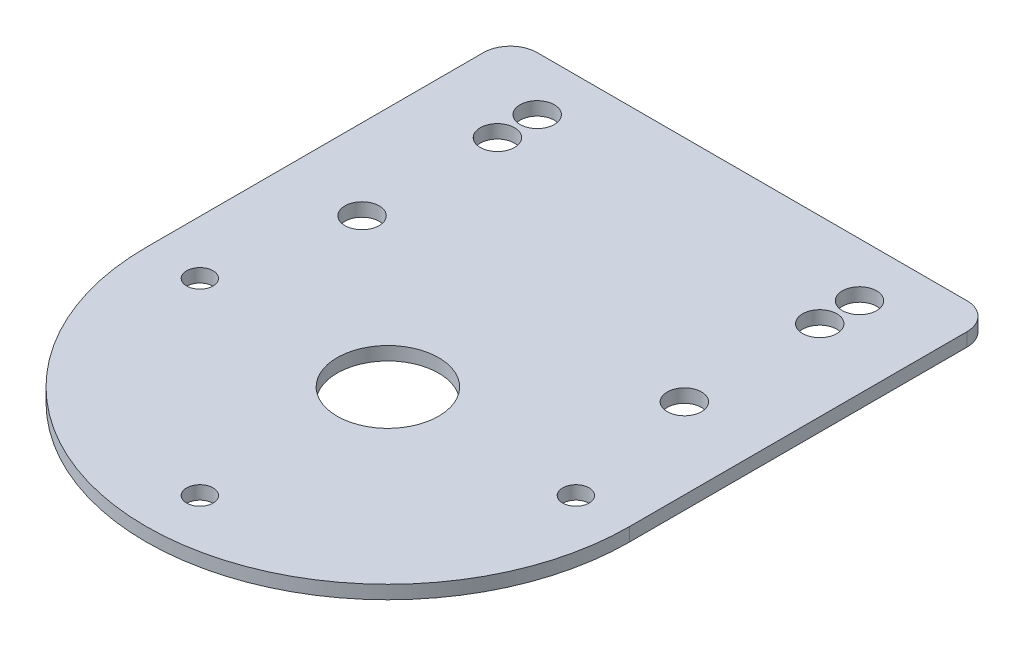
SolidWorks part; units mm, degrees
ref_plane "Front Plane" through (0, 0, 0) normal (0, 0, 1) x (1, 0, 0)
ref_plane "Top Plane" through (0, 0, 0) normal (0, 1, 0) x (1, 0, 0)
ref_plane "Right Plane" through (0, 0, 0) normal (1, 0, 0) x (0, 0, -1)
sketch "Sketch1" plane through (0, 0, 0) normal (0, 1, 0) x (1, 0, 0)
  line L0 (-28.575, 0) -> (-28.575, 39.875)
  line L1 (-25.4, 43.05) -> (25.4, 43.05)
  line L2 (28.575, 39.875) -> (28.575, 0)
  line L3 (0, 0) -> (0, 24) construction
  line L4 (-28.575, 25.4) -> (28.575, 25.4) construction
  line L5 (-19.05, 32) -> (19.05, 16) construction
  circle A0 centre (0, 0) radius 6
  circle A1 centre (0, 0) radius 13 construction
  arc A6 (-28.575, 0) -> (28.575, 0) centre (0, 0) ccw
  circle A7 centre (0, 0) radius 20 construction
  circle A8 centre (0, 0) radius 22.225 construction
  circle A9 centre (-22.225, 0) radius 1.5625
  circle A10 centre (0, -22.225) radius 1.5625
  circle A11 centre (22.225, 0) radius 1.5625
  circle A12 centre (-19.05, 16) radius 2.025
  circle A13 centre (19.05, 16) radius 2.025
  circle A14 centre (19.05, 32) radius 2.025
  circle A15 centre (-19.05, 32) radius 2.025
  circle A16 centre (-19.05, 36.7) radius 2.025
  circle A17 centre (19.05, 36.7) radius 2.025
  arc A18 (25.4, 43.05) -> (28.575, 39.875) centre (25.4, 39.875) cw
  arc A19 (-28.575, 39.875) -> (-25.4, 43.05) centre (-25.4, 39.875) cw
  point P15 (0, 0)
  point P24 (0, 0)
  point P30 (0, 22.225)
  dimension "D1" = 12
  dimension "D2" = 3.125
  dimension "D3" = 26
  dimension "D5" = 57.15
  dimension "D6" = 40
  dimension "D7" = 44.45
  dimension "D11" = 4.05
  dimension "D19" = 3.175
  dimension "D9" = 24
  dimension "D14" = 19.05
  dimension "D15" = 16
  dimension "D17" = 19.05
  dimension "D18" = 6.35
  dimension "D4" = 12.7
  dimension "D12" = 2
  dimension "D13" = 2
  dimension "D8" = 3
extrude "Boss-Extrude1" add sketch "Sketch1" along normal blind 1.5875
